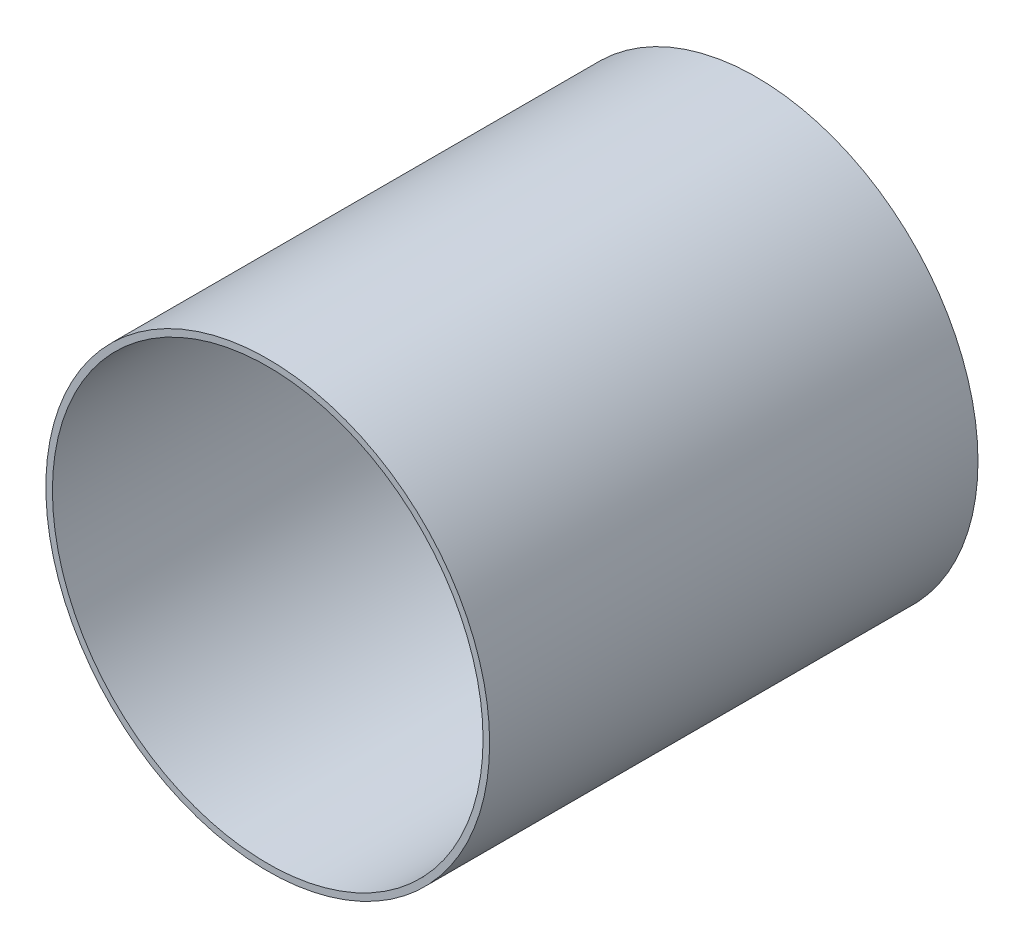
SolidWorks part; units mm, degrees
ref_plane "Front Plane" through (0, 0, 0) normal (0, 0, 1) x (1, 0, 0)
ref_plane "Top Plane" through (0, 0, 0) normal (0, 1, 0) x (1, 0, 0)
ref_plane "Right Plane" through (0, 0, 0) normal (1, 0, 0) x (0, 0, -1)
sketch "Sketch1" plane through (0, 0, 0) normal (0, 0, 1) x (1, 0, 0)
  circle A0 centre (0, 0) radius 63.4746
  circle A1 centre (0, 0) radius 61.595
  dimension "D1" = 123.19
  dimension "D2" = 126.9492
extrude "Boss-Extrude1" add sketch "Sketch1" along normal mid plane 139.7
equation "\"AIRFRAME_OD\"= 5.15in"
equation "\"AIRFRAME_ID\"= 4.99in"
equation "\"FLAT_T\"= 0.125in"
equation "\"NOSE_EXP_L\"= 27in"
equation "\"NOSE_SHOULDER_L\"= 5in"
equation "\"MAIN_L\"= 30in"
equation "\"RECO_COUP_L\"= 10in"
equation "\"RECO_SWITCH_L\"= 2in"
equation "\"DROGUE_L\"= 20in"
equation "\"ATS_FORE_COUP_L\"= 5.5in"
equation "\"ATS_AFT_COUP_L\"= 4.5in"
equation "\"LOWER_L\"= 30in"
equation "\"FIN_N\"= 4"
equation "\"CR_AFT_X\"= 0.5in"
equation "\"CR_FORE_X\"= 9.25in"
equation "\"D1@Sketch1\"=\"COUPLER_ID\""
equation "\"D2@Sketch1\"=\"COUPLER_OD\""
equation "\"D1@Boss-Extrude1\"=\"ATS_FORE_COUP_L\""
equation "\"FIN_ROOT\"= 8in"
equation "\"FIN_X\"= 0.75in"
equation "\"MOTOR_OD\"= 3.091in"
equation "\"MOTOR_ID\"= 3.00in"
equation "\"COUPLER_OD\"= 4.998in"
equation "\"COUPLER_ID\"= 4.85in"
equation "\"RECO_ROD_X\"= 3.5in"
equation "\"ATS_ROD_X\"= 3.75in"
equation "\"MOTOR_L\"= 14in"
equation "\"MOTOR_LOWER_X\"= 2in"
